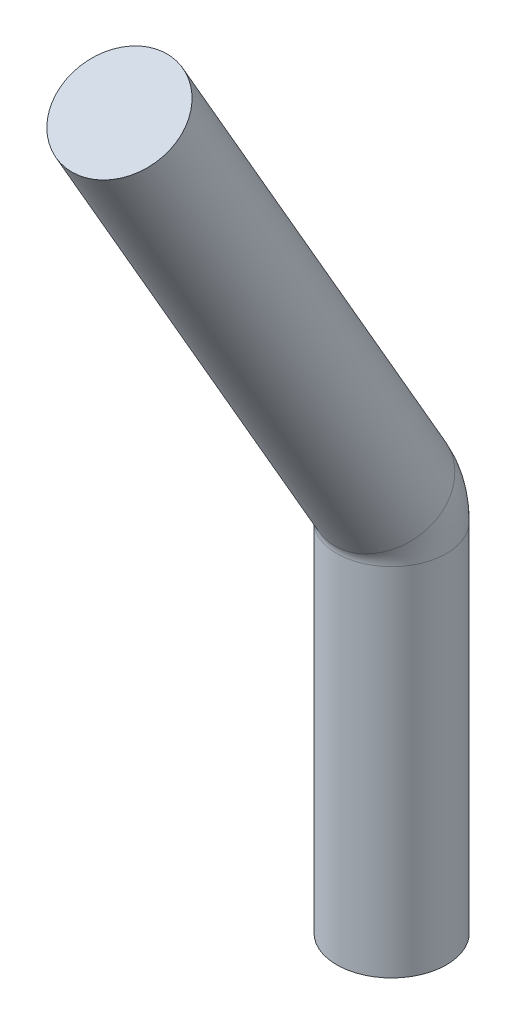
SolidWorks part; units mm, degrees
ref_plane "Front Plane" through (0, 0, 0) normal (0, 0, 1) x (1, 0, 0)
ref_plane "Top Plane" through (0, 0, 0) normal (0, 1, 0) x (1, 0, 0)
ref_plane "Right Plane" through (0, 0, 0) normal (1, 0, 0) x (0, 0, -1)
sketch "Sketch23" plane through (0, 0, 0) normal (0, 1, 0) x (1, 0, 0)
  circle A0 centre (0, 0) radius 0.47
  dimension "D1" = 0.94
sketch "Sketch24" plane through (0, 0, 0) normal (1, 0, 0) x (0, 0, -1)
  line L0 (0, 0) -> (0, 0.5)
  line L1 (0, 0.66) -> (0, -0.66) construction
  line L2 (-0.0804, 0.8) -> (-2.3304, 4.6971)
  arc A0 (0, 0.5) -> (-0.0804, 0.8) centre (-0.6, 0.5) ccw
  dimension "D1" = 0.5
  dimension "D2" = 0.6
  dimension "D3" = 30
  dimension "D4" = 4.5
sweep "Sweep4" add profiles "Sketch23" path "Sketch24"
sketch "Sketch25" plane through (0, 0, 0) normal (0, -1, 0) x (-1, 0, 0)
  circle A0 centre (0, 0) radius 0.47
  dimension "D1" = 0.94
extrude "Boss-Extrude2" add sketch "Sketch25" along normal blind 2.55
sketch "Sketch28" plane through (0, 4.5319, 2.6165) normal (0, 0.866, 0.5) x (1, 0, 0)
  line L0 (0, 0.3304) -> (0.47, 0.3304)
  circle A0 centre (0, 0.3304) radius 0.47 construction
